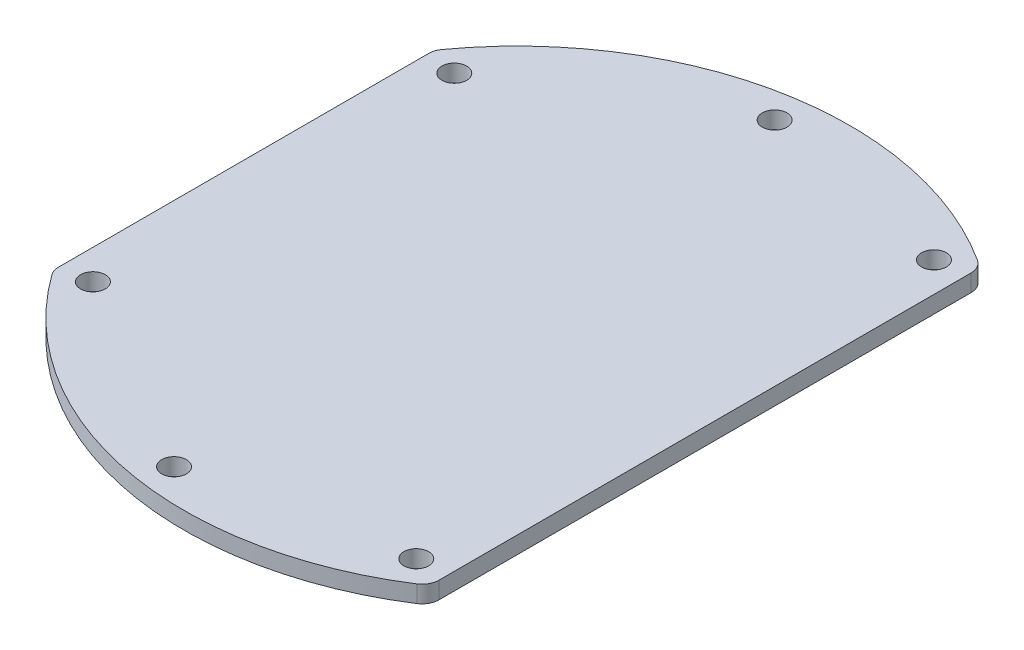
SolidWorks part; units mm, degrees
ref_plane "Front Plane" through (0, 0, 0) normal (0, 0, 1) x (1, 0, 0)
ref_plane "Top Plane" through (0, 0, 0) normal (0, 1, 0) x (1, 0, 0)
ref_plane "Right Plane" through (0, 0, 0) normal (1, 0, 0) x (0, 0, -1)
sketch "Sketch1" plane through (0, 0, 0) normal (0, 1, 0) x (1, 0, 0)
  line L1 (-32, 22.2935) -> (-32, -22.2935)
  line L2 (22, -32.2025) -> (22, 32.2025)
  line L3 (-32, 0) -> (22, 0) construction
  arc A0 (22, 32.2025) -> (-32, 22.2935) centre (0, 0) ccw
  arc A1 (-32, -22.2935) -> (22, -32.2025) centre (0, 0) ccw
  dimension "D1" = 39
  dimension "D2" = 54
  dimension "D3" = 32
extrude "Boss-Extrude1" add sketch "Sketch1" along normal blind 2
fillet "Fillet1" radius 2 4 edges at (22, 1, -32.2025) (-32, 1, -22.2935) (22, 1, 32.2025) (-32, 1, 22.2935)
hole_wizard "Ø2.9 (2.9) Diameter Hole1" positions "Sketch3" profile "Sketch4" hole size "Ø2.9" standard "ANSI Metric" end condition through all
sketch "Sketch3" plane through (0, 2, 0) normal (0, 1, 0) x (1, 0, 0)
  line L7 (22, 0) -> (-32, 0) construction
  line L8 (22, -31.1288) -> (22, 31.1288) construction
  line L9 (-32, 21.6564) -> (-32, -21.6564) construction
  point P0 (-28.5, 21.15)
  point P2 (-28.5, -21.15)
  point P4 (18.5, -30.3)
  point P6 (18.5, 30.3)
  point P8 (-5, 35.15)
  point P41 (-5, -35.15)
  point P79 (-5, 0)
  dimension "D1" = 70.3
  dimension "D2" = 42.3
  dimension "D3" = 60.6
  dimension "D4" = 3.5
  dimension "D5" = 3.5
sketch "Sketch4" plane through (-28.5, 2, -21.15) normal (1, 0, 0) x (0, 0, 1)
  line L0 (0, 0) -> (0, 2)
  line L1 (0, 2) -> (1.45, 2)
  line L2 (1.45, 2) -> (1.45, 0)
  line L5 (1.45, 0) -> (0, 0)
  line L11 (0, -6.35) -> (0, 107.95) construction
  dimension "Thru Hole Dia." = 2.9
  dimension "Thru Hole Depth" = 2
